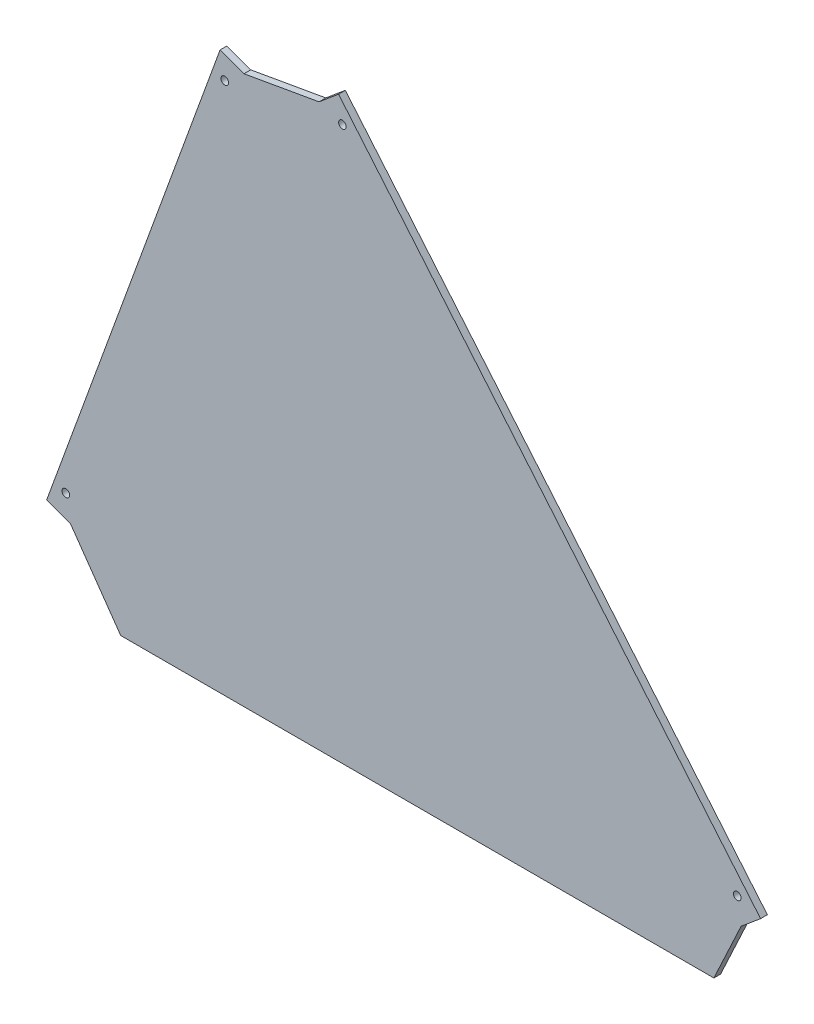
SolidWorks part; units mm, degrees
ref_plane "正面" through (0, 0, 0) normal (0, 0, 1) x (1, 0, 0)
ref_plane "平面" through (0, 0, 0) normal (0, 1, 0) x (1, 0, 0)
ref_plane "右側面" through (0, 0, 0) normal (1, 0, 0) x (0, 0, -1)
sketch "ｽｹｯﾁ1" plane through (0, 0, 0) normal (0, 0, 1) x (1, 0, 0)
  line L0 (0, 0) -> (133.1152, 365.731) construction
  line L1 (133.1152, 365.731) -> (440, 0) construction
  line L2 (440, 0) -> (0, 0) construction
  line L3 (133.1152, 365.731) -> (133.1152, 0) construction
  line L13 (117.7243, 323.4449) -> (162.0407, 331.259)
  line L14 (162.0407, 331.259) -> (411.0746, 34.472) construction
  line L15 (411.0746, 34.472) -> (395, 0)
  line L16 (395, 0) -> (45, 0)
  line L17 (45, 0) -> (15.3909, 42.2862)
  line L18 (15.3909, 42.2862) -> (117.7243, 323.4449) construction
  line L19 (117.7243, 323.4449) -> (15.3909, 42.2862)
  line L20 (117.7243, 323.4449) -> (103.6289, 328.5752)
  line L21 (15.3909, 42.2862) -> (1.2955, 47.4165)
  line L22 (103.6289, 328.5752) -> (1.2955, 47.4165)
  line L23 (162.0407, 331.259) -> (411.0746, 34.472)
  line L24 (162.0407, 331.259) -> (173.5313, 340.9009)
  line L25 (411.0746, 34.472) -> (422.5652, 44.1138)
  line L26 (173.5313, 340.9009) -> (422.5652, 44.1138)
  dimension "D4" = 45
  dimension "D5" = 45
  dimension "D6" = 45
  dimension "D9" = 45
  dimension "D10" = 15
  dimension "D1" = 440
  dimension "D2" = 70
  dimension "D3" = 50
  dimension "D7" = 45
  dimension "D8" = 45
  dimension "D11" = 15
extrude "ﾎﾞｽ - 押し出し1" add sketch "ｽｹｯﾁ1" along normal blind 4 contours L23 L13 L19 L17 L16 L15 | L20 L22 L21 L19 | L26 L24 L23 L25
sketch "ｽｹｯﾁ2" plane through (0, 0, 4) normal (0, 0, 1) x (1, 0, 0)
  line L0 (103.6289, 328.5752) -> (1.2955, 47.4165) construction
  line L1 (15.3909, 42.2862) -> (1.2955, 47.4165) construction
  line L2 (117.7243, 323.4449) -> (103.6289, 328.5752) construction
  line L3 (173.5313, 340.9009) -> (422.5652, 44.1138) construction
  line L4 (162.0407, 331.259) -> (173.5313, 340.9009) construction
  line L5 (411.0746, 34.472) -> (422.5652, 44.1138) construction
  point P0 (106.4014, 314.2639)
  point P1 (12.6185, 56.5975)
  point P2 (175.8208, 326.5044)
  point P3 (408.785, 48.8685)
  dimension "D1" = 7.5
  dimension "D2" = 7.5
  dimension "D3" = 12.5
  dimension "D4" = 12.5
  dimension "D5" = 7.5
  dimension "D6" = 7.5
  dimension "D7" = 12.5
  dimension "D8" = 12.5
hole_wizard "M4 すきま穴1" positions "ｽｹｯﾁ2" profile "ｽｹｯﾁ3" hole size "M4" standard "JIS" end condition through all
sketch "ｽｹｯﾁ3" plane through (106.4014, 314.2639, 4) normal (1, 0, 0) x (0, -1, 0)
  line L0 (0, 0) -> (0, 4)
  line L1 (0, 4) -> (2.25, 4)
  line L2 (2.25, 4) -> (2.25, 0)
  line L5 (2.25, 0) -> (0, 0)
  line L11 (0, -6.35) -> (0, 107.95) construction
  dimension "通し穴の直径" = 4.5
  dimension "通し穴の深さ" = 4
